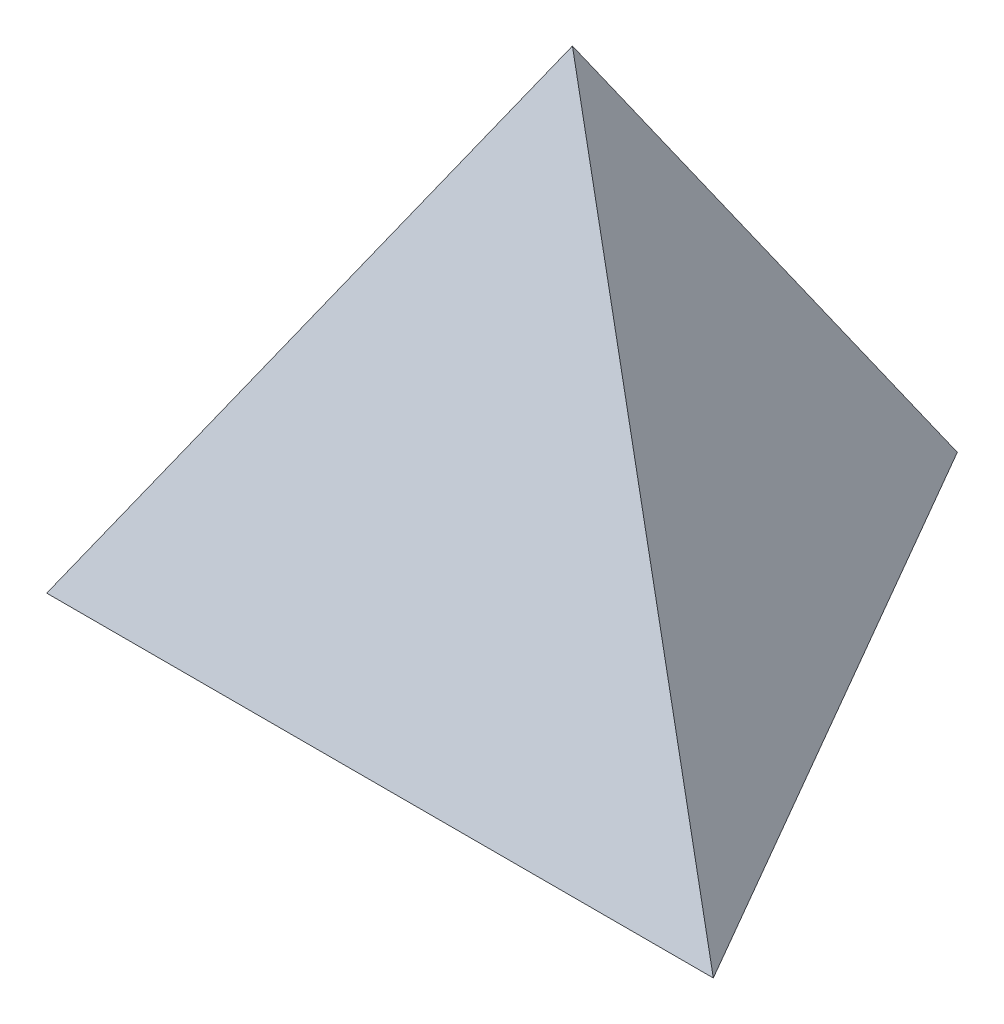
SolidWorks part; units mm, degrees
ref_plane "Front Plane" through (0, 0, 0) normal (0, 0, 1) x (1, 0, 0)
ref_plane "Top Plane" through (0, 0, 0) normal (0, 1, 0) x (1, 0, 0)
ref_plane "Right Plane" through (0, 0, 0) normal (1, 0, 0) x (0, 0, -1)
sketch "Sketch1" plane through (0, 0, 0) normal (0, 1, 0) x (1, 0, 0)
  line L0 (-25.4, -14.6647) -> (25.4, -14.6647)
  line L1 (25.4, -14.6647) -> (0, 29.3294)
  line L2 (0, 29.3294) -> (-25.4, -14.6647)
  line L3 (-25.4, -14.6647) -> (0, 0) construction
  line L4 (0, 0) -> (25.4, -14.6647) construction
  line L5 (0, 29.3294) -> (0, 0) construction
  point P2 (0, -14.6647)
  dimension "D1" = 50.8
sketch3d "3DSketch1"
  line L0 (-25.4, 0, 14.6647) -> (0, 41.478, 0)
  line L1 (0, 0, -29.3294) -> (-25.4, 0, 14.6647) construction
  line L2 (0, 41.478, 0) -> (25.4, 0, 14.6647)
  line L3 (0, 41.478, 0) -> (0, 0, -29.3294)
extrude "Boss-Extrude1" add sketch "Sketch1" along direction (0, -0.8165, -0.5774) on the side of the normal up to vertex (41.478 mm away) contours L1 L2 L0
ref_plane "Plane1" through (0, 4.6087, 13.0353) normal (0, 0.3333, 0.9428) x (1, 0, 0)
other "SurfaceCut1"
